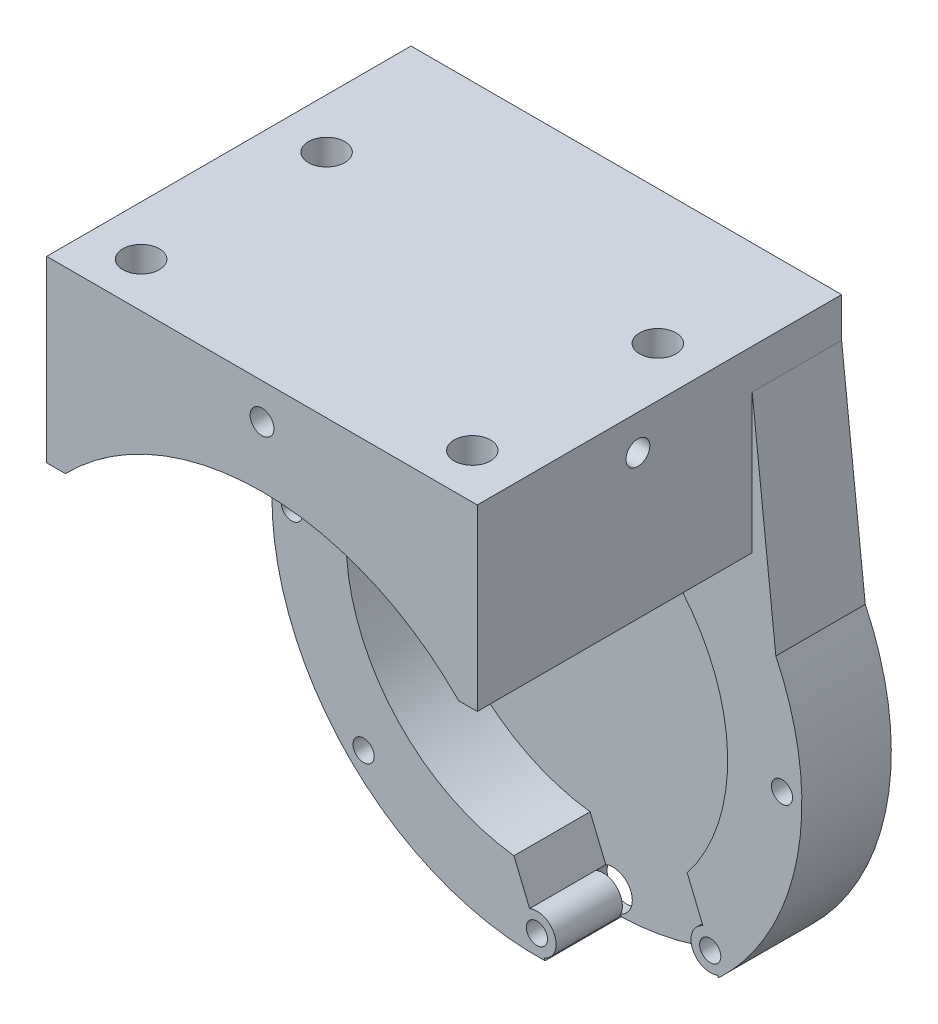
SolidWorks part; units mm, degrees
other "标注1"
sketch "草图20" plane through (-40, 128, 27.5) normal (-0.9349, 0.1755, 0.3084) x (0.3368, 0.1651, 0.927)
ref_plane "前视基准面" through (0, 0, 0) normal (0, 0, 1) x (1, 0, 0)
ref_plane "上视基准面" through (0, 0, 0) normal (0, 1, 0) x (1, 0, 0)
ref_plane "右视基准面" through (0, 0, 0) normal (1, 0, 0) x (0, 0, -1)
other "Configuration Table"
ref_plane "基准面1" through (0, 0, -14) normal (0, 0, 1) x (1, 0, 0)
sketch "草图1" plane through (0, 0, -14) normal (0, 0, 1) x (1, 0, 0)
  line L3 (36.0707, 17.2888) -> (32.5, 50)
  line L4 (-36.0707, 17.2888) -> (-32.5, 50)
  line L5 (-32.5, 50) -> (32.5, 50)
  arc A0 (-36.0707, 17.2888) -> (36.0707, 17.2888) centre (0, 0) ccw
extrude "凸台-拉伸1" add sketch "草图1" against normal blind 13.5
sketch "草图2" plane through (0, 0, -14) normal (0, 0, 1) x (1, 0, 0)
  circle A0 centre (0, 0) radius 28.8
extrude "切除-拉伸1" cut sketch "草图2" against normal blind 11.5
sketch "草图3" plane through (0, 0, -27.5) normal (0, 0, -1) x (-1, 0, 0)
  circle A1 centre (0, 37) radius 1.6
extrude "切除-拉伸2" cut sketch "草图3" against normal through all
sketch "草图6" plane through (0, 0, -27.5) normal (0, 0, -1) x (-1, 0, 0)
  circle A0 centre (0, 37) radius 2.9
  circle A1 centre (26.163, 26.163) radius 2.9
  circle A2 centre (37, 0) radius 2.9
  circle A3 centre (26.163, -26.163) radius 2.9
  circle A6 centre (-37, 0) radius 2.9
  circle A7 centre (-26.163, 26.163) radius 2.9
  circle A8 centre (-26.163, -26.163) radius 2.9 [skipped]
  circle A9 centre (0, -37) radius 2.9 [skipped]
  circle A10 centre (0, -37) radius 2.9
  circle A11 centre (-26.163, -26.163) radius 2.9
  point P15 (0, 0)
  point P20 (0, 0)
  dimension "D1" = 8
  dimension "D2" = 3
extrude "切除-拉伸6" cut sketch "草图6" against normal blind 3.5
pattern_circular "阵列(圆周)3" count 8 every 45 about axis through (0, 0, 0) along (0, 0, 1) of "切除-拉伸2"
ref_plane "基准面3" through (0, 40, 0) normal (0, 1, 0) x (1, 0, 0)
sketch "草图7" plane through (0, 40, 0) normal (0, 1, 0) x (1, 0, 0)
  line L5 (-32.5, 0) -> (-32.5, 16.2834)
  line L7 (32.5, 0) -> (32.5, 16.2834)
  line L9 (-32.5, 0) -> (-32.5, -27.5)
  line L10 (0, -27.5) -> (-32.5, -27.5)
  line L11 (32.5, 0) -> (32.5, -27.5)
  line L12 (32.5, -27.5) -> (0, -27.5)
  line L13 (-32.5, 16.2834) -> (-32.5, 27.5)
  line L14 (-32.5, 27.5) -> (-5.851, 27.5)
  line L15 (32.5, 27.5) -> (32.5, 16.2834)
  line L18 (5.654, 27.5) -> (32.5, 27.5)
  line L26 (-5.851, 27.5) -> (-5.851, 14)
  line L27 (32.5, 14) -> (-32.5, 14) construction
  line L28 (-5.851, 14) -> (5.654, 14)
  line L29 (5.654, 14) -> (5.654, 27.5)
extrude "凸台-拉伸2" add sketch "草图7" along normal blind 10 and the other way blind 11 separate body
sketch "草图9" plane through (0, 0, -14) normal (0, 0, 1) x (1, 0, 0)
  line L0 (-31.3063, 27.2427) -> (31.3063, 27.2427)
  arc A0 (31.3063, 27.2427) -> (-31.3063, 27.2427) centre (0, 0) ccw
extrude "切除-拉伸7" cut sketch "草图9" along normal through all
sketch "草图25" plane through (0, 50, 0) normal (0, 1, 0) x (1, 0, 0)
  line L1 (-32.5, 27.5) -> (32.5, 27.5)
  line L2 (-32.5, 27.5) -> (-32.5, -27.5)
  line L4 (32.5, 27.5) -> (32.5, -27.5)
  line L5 (-32.5, -27.5) -> (32.5, -27.5)
  line L6 (-32.5, -27.5) -> (32.5, -27.5) construction
extrude "凸台-拉伸4" add sketch "草图25" along normal blind 6
sketch "草图33" plane through (0, 56, 0) normal (0, 1, 0) x (1, 0, 0)
  circle A0 centre (-25, 7.25) radius 2.75
  circle A1 centre (25, 7.25) radius 2.75
  circle A2 centre (-25, -20.75) radius 2.75
  circle A3 centre (25, -20.75) radius 2.75
extrude "切除-拉伸14" cut sketch "草图33" against normal through all
ref_plane "基准面5" through (0, 46, 0) normal (0, 1, 0) x (1, 0, 0)
sketch "草图34" plane through (0, 46, 0) normal (0, 1, 0) x (1, 0, 0)
  circle A0 centre (-25, 7.25) radius 5
  circle A1 centre (25, 7.25) radius 5
  circle A2 centre (-25, -20.75) radius 5
  circle A3 centre (25, -20.75) radius 5
extrude "切除-拉伸15" cut sketch "草图34" against normal through all
ref_plane "基准面6" through (0, 0, -25.5) normal (0, 0, 1) x (1, 0, 0)
sketch "草图35" plane through (0, 0, -25.5) normal (0, 0, 1) x (1, 0, 0)
  line L0 (-5.4823, -23.6958) -> (20.7004, -12.9066)
  line L4 (-1.1049, -34.3187) -> (-5.4823, -23.6958)
  line L5 (25.0581, -23.4817) -> (20.7004, -12.9066)
  line L6 (27.2678, -28.8442) -> (28.6382, -32.1697)
  line L7 (1.1049, -39.6813) -> (2.4654, -42.9828)
  line L8 (2.4654, -42.9828) -> (28.6382, -32.1697)
  arc A0 (1.1049, -39.6813) -> (-1.1049, -34.3187) centre (0, -37) ccw
  arc A1 (25.0581, -23.4817) -> (27.2678, -28.8442) centre (26.163, -26.163) ccw
extrude "切除-拉伸16" cut sketch "草图35" along normal through all
sketch "草图40" plane through (0, 0, 27.5) normal (0, 0, 1) x (1, 0, 0)
  circle A0 centre (0, 50.6086) radius 1.8
extrude "切除-拉伸18" cut sketch "草图40" against normal blind 12
sketch "草图41" plane through (-37.511, 4.0947, 0) normal (-0.9941, 0.1085, 0) x (0, 0, 1)
  circle A0 centre (-20.75, 29.9799) radius 1.8
extrude "切除-拉伸19" cut sketch "草图41" against normal blind 12
sketch "草图42" plane through (32.5, 0, 0) normal (1, 0, 0) x (0, 0, -1)
  circle A0 centre (-3.2545, 50.7181) radius 1.8
extrude "切除-拉伸20" cut sketch "草图42" against normal blind 12
sketch "草图43" plane through (-32.5, 0, 0) normal (-1, 0, 0) x (0, 0, 1)
  circle A0 centre (2.4897, 51.6006) radius 1.8
extrude "切除-拉伸21" cut sketch "草图43" against normal blind 12
